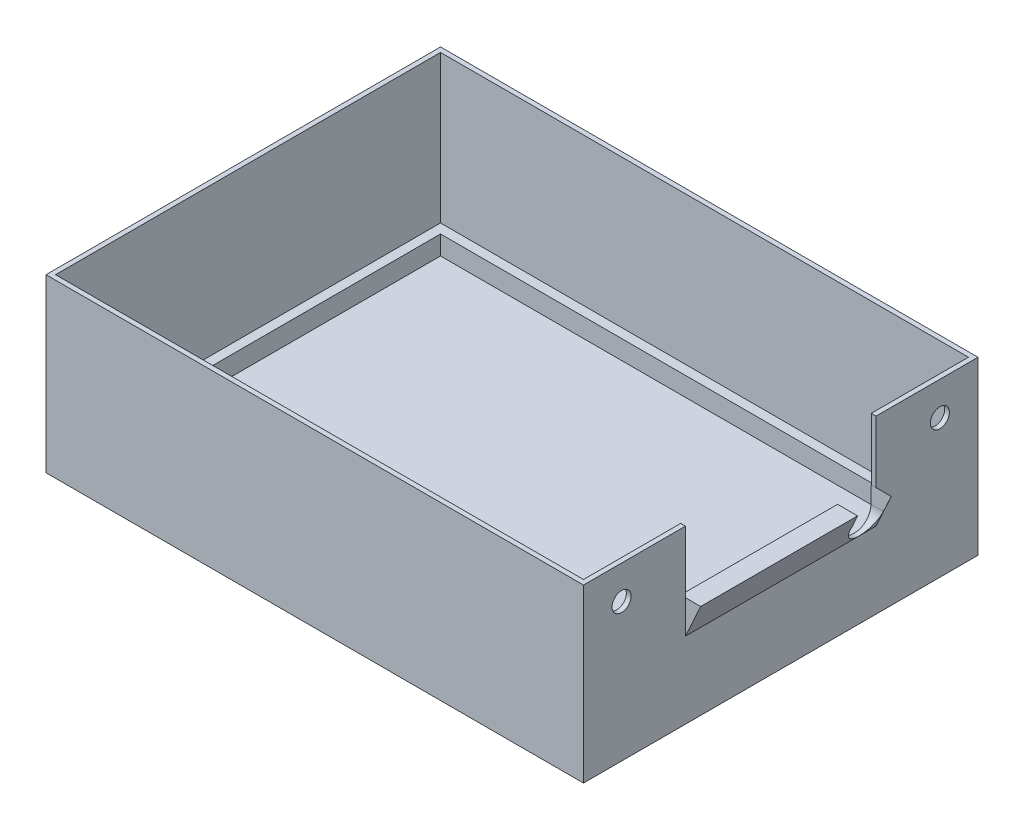
SolidWorks part; units mm, degrees
ref_plane "Front Plane" through (0, 0, 0) normal (0, 0, 1) x (1, 0, 0)
ref_plane "Top Plane" through (0, 0, 0) normal (0, 1, 0) x (1, 0, 0)
ref_plane "Right Plane" through (0, 0, 0) normal (1, 0, 0) x (0, 0, -1)
sketch "Sketch1" plane through (0, 0, 0) normal (0, 1, 0) x (1, 0, 0)
  line L1 (-89.7958, 44.0317) -> (23.0042, 44.0317)
  line L2 (-89.7958, 44.0317) -> (-89.7958, -38.7683)
  line L3 (-89.7958, -38.7683) -> (23.0042, -38.7683)
  line L4 (23.0042, 44.0317) -> (23.0042, -38.7683)
  dimension "D1" = 82.8
  dimension "D2" = 112.8
extrude "Boss-Extrude2" add sketch "Sketch1" along normal blind 36
shell "Shell1" thickness 1
sketch "Sketch2" plane through (0, 1, 0) normal (0, 1, 0) x (1, 0, 0)
  line L1 (-88.7958, 43.0317) -> (22.0042, 43.0317)
  line L2 (-88.7958, 43.0317) -> (-88.7958, -37.7683)
  line L3 (-88.7958, -37.7683) -> (22.0042, -37.7683)
  line L4 (22.0042, 43.0317) -> (22.0042, -37.7683)
  line L5 (-86.7958, 41.0317) -> (20.0042, 41.0317)
  line L6 (-86.7958, 41.0317) -> (-86.7958, -35.7683)
  line L7 (-86.7958, -35.7683) -> (20.0042, -35.7683)
  line L8 (20.0042, 41.0317) -> (20.0042, -35.7683)
  dimension "D1" = 2
  dimension "D2" = 2
  dimension "D3" = 2
  dimension "D4" = 2
extrude "Boss-Extrude3" add sketch "Sketch2" along normal blind 4
sketch "Sketch3" plane through (23.0042, 0, 0) normal (1, 0, 0) x (0, 0, -1)
  line L0 (2.6317, 36) -> (2.6317, 0) construction
  line L1 (-38.7683, 36) -> (44.0317, 36) construction
  line L2 (-38.7683, 0) -> (44.0317, 0) construction
  line L4 (-17.3683, 36) -> (22.6317, 36)
  line L5 (-17.3683, 36) -> (-17.3683, 23)
  line L6 (-17.3683, 23) -> (22.6317, 23)
  line L7 (22.6317, 36) -> (22.6317, 23)
  dimension "D1" = 40
  dimension "D2" = 13
extrude "Cut-Extrude1" cut sketch "Sketch3" against normal up to next contours L5 L4 L7 L6
sketch "Sketch4" plane through (0, 0, -22.6317) normal (0, 0, 1) x (1, 0, 0)
  line L0 (23.0042, 23) -> (23.0042, 16)
  line L1 (23.0042, 23) -> (26.2042, 23)
  line L2 (26.2042, 23) -> (23.0042, 16)
extrude "Boss-Extrude4" add sketch "Sketch4" along normal up to vertex (40 mm away) contours L2 L0 L1
sketch "Sketch6" plane through (22.0042, 0, 0) normal (-1, 0, 0) x (0, 0, 1)
  line L0 (17.3683, 23) -> (-22.6317, 23) construction
  line L1 (-22.5605, 19.5) -> (-22.6317, 23)
  line L2 (-22.6317, 23) -> (-15.5605, 23)
  line L3 (-15.5605, 23) -> (-15.5605, 19.5)
  arc A0 (-22.5605, 19.5) -> (-15.5605, 19.5) centre (-19.0605, 19.5) ccw
  point P1 (-22.5317, 16.6779)
  point P11 (0, 0)
  line M2 (17.3683, 23) -> (-22.6317, 23)
extrude "Cut-Extrude2" cut sketch "Sketch6" against normal up to next contours L1 A0 L3 M2
sketch "Sketch7" plane through (23.0042, 0, 0) normal (1, 0, 0) x (0, 0, -1)
  line L0 (22.6317, 36) -> (44.0317, 36) construction
  line L1 (44.0317, 36) -> (44.0317, 0) construction
  line L2 (2.6317, 36) -> (2.6317, 0) construction
  line L3 (43.0317, 36) -> (-37.7683, 36) construction
  line L4 (-38.7683, 0) -> (44.0317, 0) construction
  circle A0 centre (36.0317, 29) radius 2
  circle A1 centre (-30.7683, 29) radius 2
  dimension "D1" = 7
  dimension "D2" = 8
extrude "Cut-Extrude3" cut sketch "Sketch7" against normal up to next
